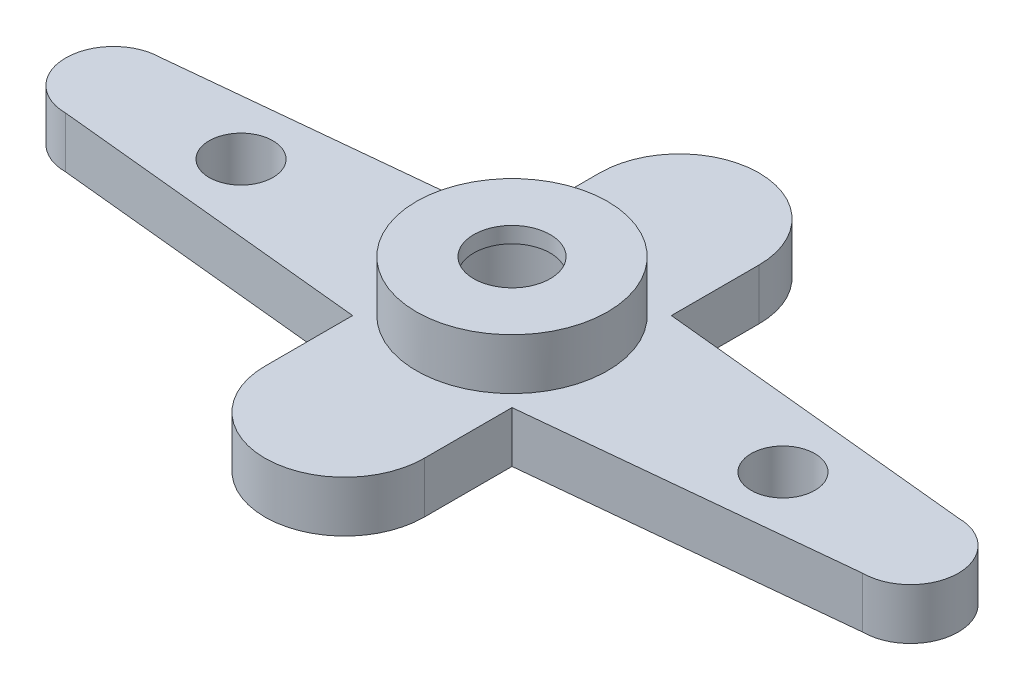
SolidWorks part; units mm, degrees
material "Galvanized Steel"
ref_plane "Front Plane" through (0, 0, 0) normal (0, 0, 1) x (1, 0, 0)
ref_plane "Top Plane" through (0, 0, 0) normal (0, 1, 0) x (1, 0, 0)
ref_plane "Right Plane" through (0, 0, 0) normal (1, 0, 0) x (0, 0, -1)
sketch "Sketch1" plane through (0, 0, 0) normal (0, 1, 0) x (1, 0, 0)
  line L0 (0, 82.722) -> (0, -84.0509) construction
  line L1 (-29.5673, 0) -> (39.866, 0) construction
  line L2 (-12.5, 12.5) -> (12.5, 12.5) construction
  line L3 (12.5, 12.5) -> (12.5, 26.25)
  line L4 (12.5, 26.25) -> (-12.5, 26.25) construction
  line L5 (-12.5, 26.25) -> (-12.5, 12.5)
  line L6 (12.5, -26.25) -> (-12.5, -26.25) construction
  line L7 (-12.5, -12.5) -> (12.5, -12.5) construction
  line L8 (-12.5, -26.25) -> (-12.5, -12.5)
  line L9 (12.5, -12.5) -> (12.5, -26.25)
  line L10 (-62.5, -7.5) -> (-62.5, 7.5) construction
  line L11 (-12.5, 12.5) -> (-62.5, 7.5)
  line L12 (-62.5, -7.5) -> (-12.5, -12.5)
  line L13 (62.5, 7.5) -> (62.5, -7.5) construction
  line L14 (12.5, 12.5) -> (62.5, 7.5)
  line L15 (62.5, -7.5) -> (12.5, -12.5)
  circle A0 centre (0, 0) radius 10
  arc A1 (12.5, 26.25) -> (-12.5, 26.25) centre (0, 26.25) ccw
  arc A2 (-12.5, -26.25) -> (12.5, -26.25) centre (0, -26.25) ccw
  arc A3 (-62.5, -7.5) -> (-62.5, 7.5) centre (-62.5, 0) cw
  arc A4 (62.5, 7.5) -> (62.5, -7.5) centre (62.5, 0) cw
  point P7 (12.5, 19.375)
  point P10 (0, 12.5)
  point P18 (0, -12.5)
  point P23 (-62.5, 0)
  point P28 (62.5, 0)
  dimension "D1" = 20
  dimension "D2" = 12.5
  dimension "D3" = 25
  dimension "D4" = 26.25
  dimension "D5" = 15
  dimension "D6" = 62.5
  dimension "D7" = 62.5
extrude "Boss-Extrude1" add sketch "Sketch1" along normal mid plane 8
sketch "Sketch2" plane through (0, 4, 0) normal (0, 1, 0) x (1, 0, 0)
  circle A0 centre (0, 0) radius 15
  circle A3 centre (0, 0) radius 10
  dimension "D1" = 30
  dimension "D2" = 20
extrude "Boss-Extrude2" add sketch "Sketch2" along normal blind 8
sketch "Sketch3" plane through (0, 4, 0) normal (0, 1, 0) x (1, 0, 0)
  line L0 (-79.2105, 0) -> (78.9841, 0) construction
  line L1 (0, 52.4138) -> (0, -71.009) construction
  circle A0 centre (42.5, 0) radius 5
  circle A1 centre (-42.5, 0) radius 5
  dimension "D1" = 10
  dimension "D2" = 85
extrude "Cut-Extrude1" cut sketch "Sketch3" against normal through all
sketch "Sketch4" plane through (0, 0, 0) normal (0, 1, 0) x (1, 0, 0)
  circle A0 centre (0, 0) radius 10
  circle A1 centre (0, 0) radius 10 construction
  circle A2 centre (0, 0) radius 6
  dimension "D1" = 12
extrude "Boss-Extrude3" add sketch "Sketch4" along normal blind 2.5 from offset 9.5
